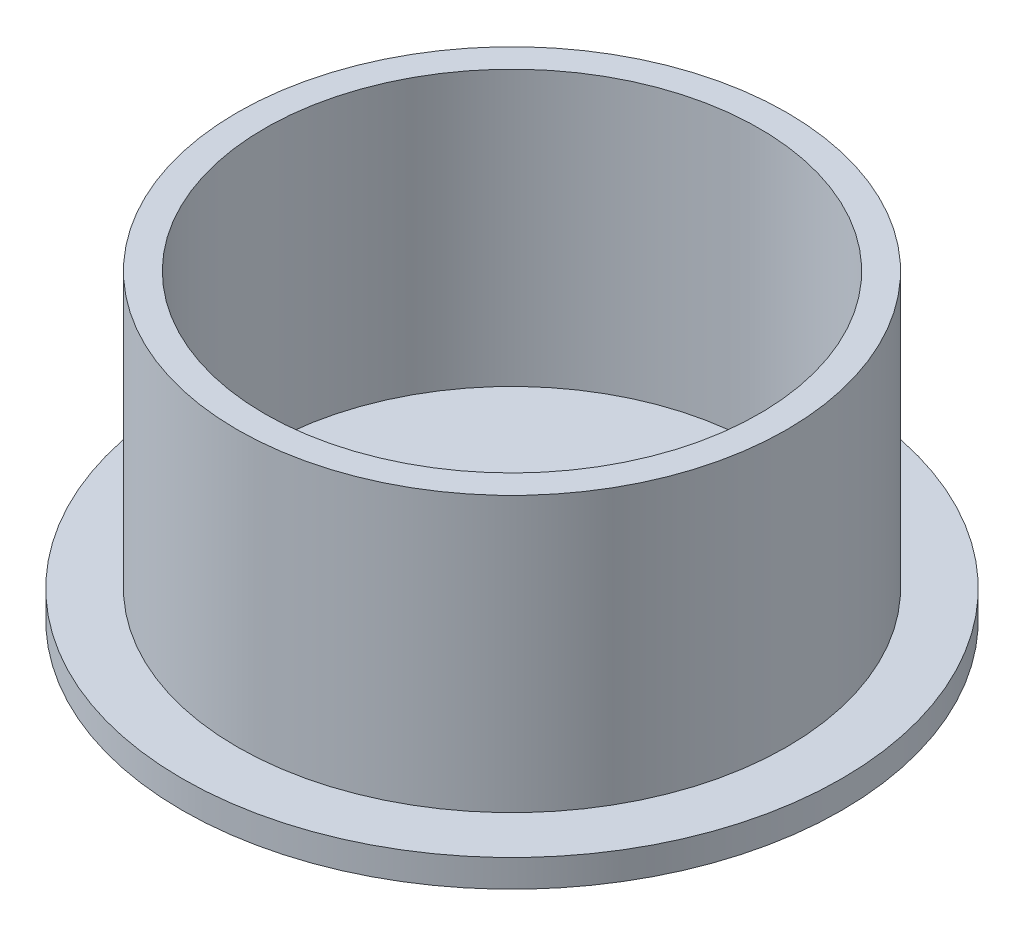
SolidWorks part; units mm, degrees
ref_plane "Front Plane" through (0, 0, 0) normal (0, 0, 1) x (1, 0, 0)
ref_plane "Top Plane" through (0, 0, 0) normal (0, 1, 0) x (1, 0, 0)
ref_plane "Right Plane" through (0, 0, 0) normal (1, 0, 0) x (0, 0, -1)
sketch "Sketch1" plane through (0, 0, 0) normal (0, 1, 0) x (1, 0, 0)
  circle A0 centre (0, 0) radius 60
  dimension "D1" = 120
extrude "Boss-Extrude1" add sketch "Sketch1" along normal blind 5
sketch "Sketch2" plane through (0, 5, 0) normal (0, 1, 0) x (1, 0, 0)
  circle A0 centre (0, 0) radius 50
  circle A1 centre (0, 0) radius 45
  dimension "D1" = 100
  dimension "D2" = 5
extrude "Boss-Extrude2" add sketch "Sketch2" along normal blind 50
sketch "Sketch3" plane through (0, 5, 0) normal (0, 1, 0) x (1, 0, 0)
  line L0 (-22.3617, -39.0507) -> (-5.483, -9.5751)
  circle A0 centre (0, 0) radius 45 construction
equation "\"5c\"=5"
